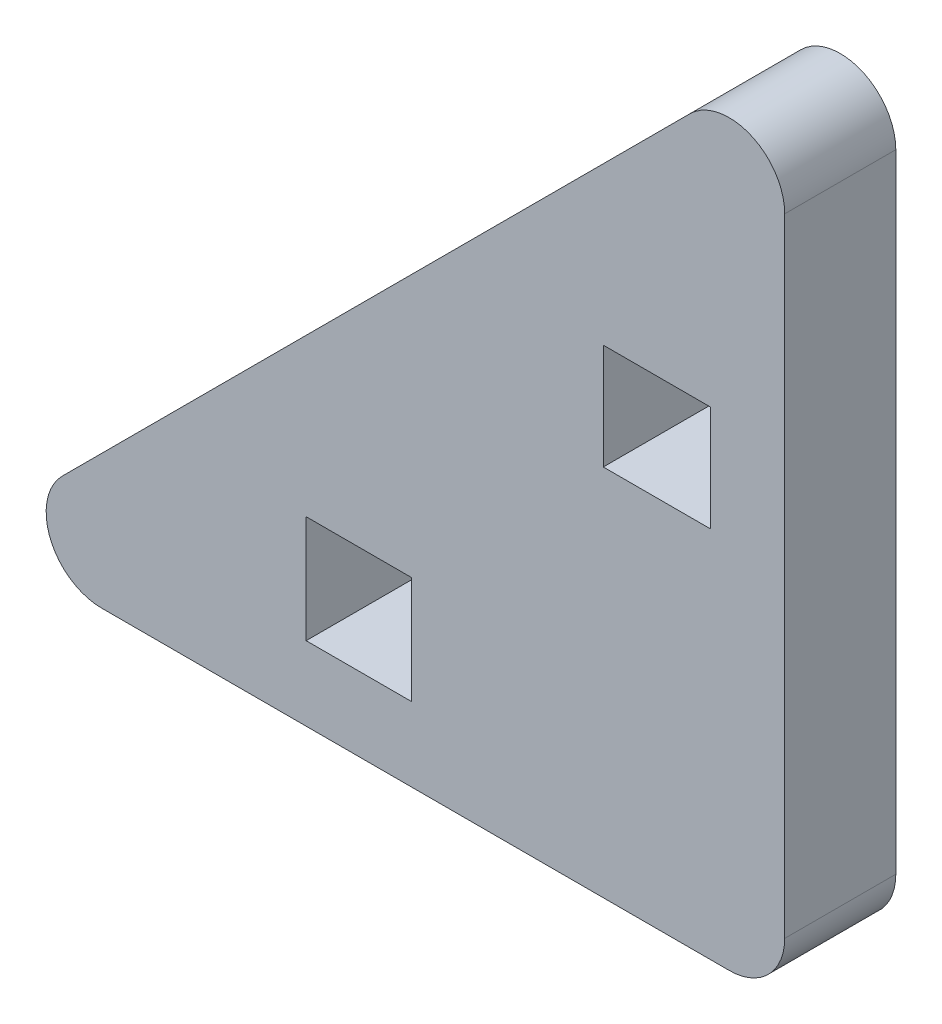
SolidWorks part; units mm, degrees
ref_plane "Спереди" through (0, 0, 0) normal (0, 0, 1) x (1, 0, 0)
ref_plane "Сверху" through (0, 0, 0) normal (0, 1, 0) x (1, 0, 0)
ref_plane "Справа" through (0, 0, 0) normal (1, 0, 0) x (0, 0, -1)
sketch "Эскиз1" plane through (0, 0, 0) normal (0, 0, 1) x (1, 0, 0)
  line L0 (0, 0) -> (-22.0676, 0)
  line L1 (-22.0676, 0) -> (0, 22.0676)
  line L2 (0, 22.0676) -> (0, 0)
  line L3 (-12.925, 2) -> (-10.075, 2)
  line L8 (-4.9, 10.075) -> (-2, 10.075)
  line L9 (-4.9, 10.075) -> (-4.9, 12.925)
  line L10 (-4.9, 12.925) -> (-2, 12.925)
  line L11 (-2, 10.075) -> (-2, 12.925)
  line L12 (-4.9, 10.075) -> (-2, 12.925) construction
  line L13 (-4.9, 12.925) -> (-2, 10.075) construction
  line L14 (-12.925, 2) -> (-12.925, 4.9)
  line L15 (-12.925, 4.9) -> (-10.075, 4.9)
  line L16 (-10.075, 2) -> (-10.075, 4.9)
  line L17 (-12.925, 2) -> (-10.075, 4.9) construction
  line L18 (-12.925, 4.9) -> (-10.075, 2) construction
  point P2 (-3.45, 11.5)
  point P8 (-11.5, 3.45)
  dimension "D1" = 2.9
  dimension "D2" = 2.85
  dimension "D3" = 2
  dimension "D4" = 2
  dimension "D5" = 9.5
  dimension "D6" = 9.5
  dimension "D7" = 3
extrude "Бобышка-Вытянуть1" add sketch "Эскиз1" along normal blind 3 contours L2 L1 L0 L16 L3 L14 L15 L11 L8 L9 L10
fillet "Скругление1" radius 1.5 3 edges at (0, 0, 1.5) (-22.0676, 0, 1.5) (0, 22.0676, 1.5)
